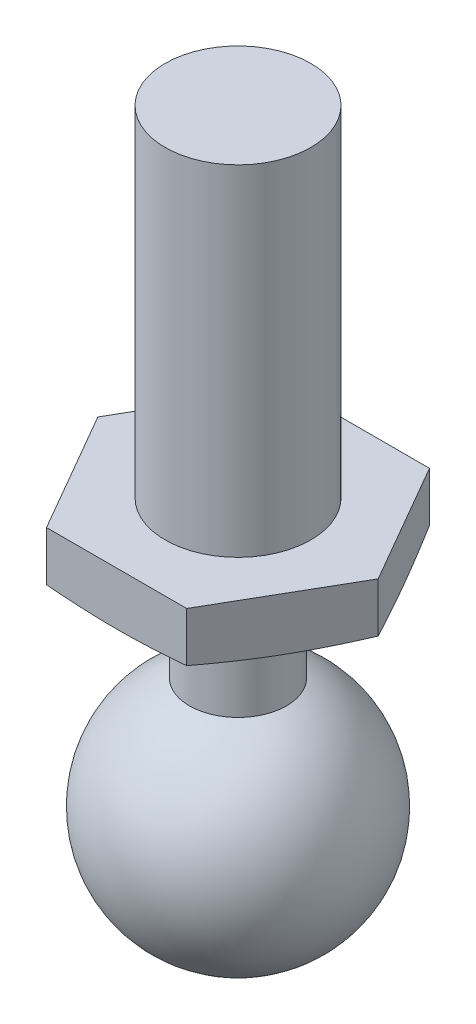
SolidWorks part; units mm, degrees
ref_plane "Front Plane" through (0, 0, 0) normal (0, 0, 1) x (1, 0, 0)
ref_plane "Top Plane" through (0, 0, 0) normal (0, 1, 0) x (1, 0, 0)
ref_plane "Right Plane" through (0, 0, 0) normal (1, 0, 0) x (0, 0, -1)
sketch "Sketch1" plane through (0, 0, 0) normal (1, 0, 0) x (0, 0, -1)
  line L0 (0, 7) -> (1.5, 7)
  line L1 (1.5, 7) -> (1.5, 0)
  line L2 (1.5, 0) -> (3, 0)
  line L3 (3, 0) -> (3, -1)
  line L5 (1, -1.3527) -> (1, -3.2087)
  line L6 (0, -8) -> (0, 7)
  line L7 (3, -1) -> (1, -1.3527)
  arc A0 (0, -8) -> (1, -3.2087) centre (0, -5.5) ccw
  dimension "D2" = 2.5
  dimension "D1" = 7
  dimension "D3" = 1
  dimension "D4" = 15
  dimension "D5" = 1
  dimension "D6" = 1.5
  dimension "2,5" = 3
  dimension "D7" = 10
revolve "Revolve1" add sketch "Sketch1" angle 360 about L6
sketch "Sketch2" plane through (0, 0, 0) normal (0, 1, 0) x (1, 0, 0)
  line L1 (1.4434, 2.5) -> (-1.4434, 2.5)
  line L2 (-1.4434, 2.5) -> (-2.8868, 0)
  line L3 (-2.8868, 0) -> (-1.4434, -2.5)
  line L4 (-1.4434, -2.5) -> (1.4434, -2.5)
  line L5 (1.4434, -2.5) -> (2.8868, 0)
  line L6 (2.8868, 0) -> (1.4434, 2.5)
  circle A0 centre (0, 0) radius 2.5 construction
  point P1 (0, 2.5)
  dimension "D1" = 5
extrude "Cut-Extrude1" cut sketch "Sketch2" against normal blind 2 flip side to cut
ref_plane "Plane1" through (0, -8, 0) normal (0, 1, 0) x (1, 0, 0)
